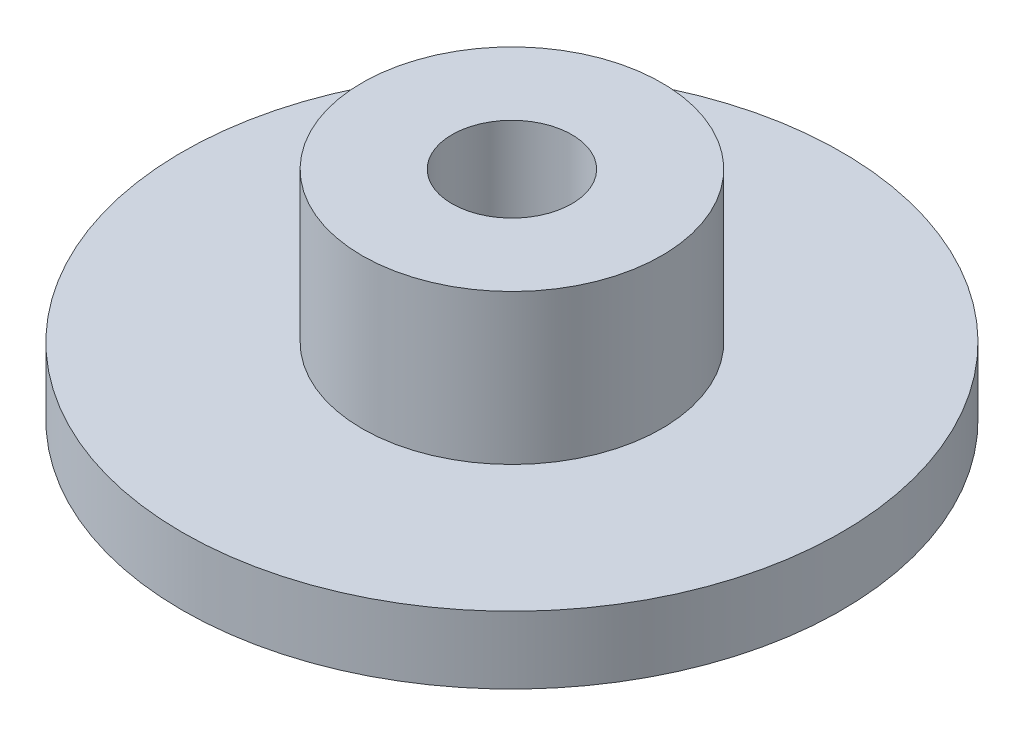
SolidWorks part; units mm, degrees
material "Stainless Steel (ferritic)"
ref_plane "Front Plane" through (0, 0, 0) normal (0, 0, 1) x (1, 0, 0)
ref_plane "Top Plane" through (0, 0, 0) normal (0, 1, 0) x (1, 0, 0)
ref_plane "Right Plane" through (0, 0, 0) normal (1, 0, 0) x (0, 0, -1)
sketch "Sketch1" plane through (0, 0, 0) normal (0, 1, 0) x (1, 0, 0)
  circle A0 centre (0, 0) radius 22
extrude "Boss-Extrude1" add sketch "Sketch1" along normal blind 4.5 contours A0
sketch "Sketch3" plane through (0, 4.5, 0) normal (0, 1, 0) x (1, 0, 0)
  circle A0 centre (0, 0) radius 10
extrude "Boss-Extrude2" add sketch "Sketch3" along normal blind 10
sketch "Sketch4" plane through (0, 14.5, 0) normal (0, 1, 0) x (1, 0, 0)
  circle A0 centre (0, 0) radius 4
extrude "Cut-Extrude1" cut sketch "Sketch4" against normal blind 15
